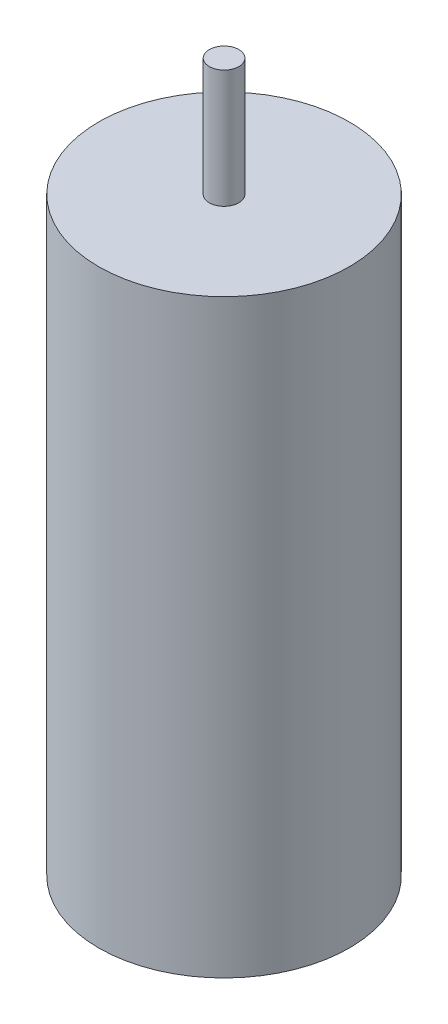
SolidWorks part; units mm, degrees
ref_plane "Front Plane" through (0, 0, 0) normal (0, 0, 1) x (1, 0, 0)
ref_plane "Top Plane" through (0, 0, 0) normal (0, 1, 0) x (1, 0, 0)
ref_plane "Right Plane" through (0, 0, 0) normal (1, 0, 0) x (0, 0, -1)
sketch "Sketch1" plane through (0, 0, 0) normal (0, 1, 0) x (1, 0, 0)
  circle A0 centre (0, 0) radius 4.25
extrude "Boss-Extrude1" add sketch "Sketch1" along normal blind 20
sketch "Sketch2" plane through (0, 20, 0) normal (0, 1, 0) x (1, 0, 0)
  circle A0 centre (0, 0) radius 0.5
extrude "Boss-Extrude2" add sketch "Sketch2" along normal blind 4
sketch3d "URDF Reference"
  line L0 (0, 0, 0) -> (10, 0, 0) construction
  line L1 (0, 0, 0) -> (0, 0, -10) construction
  point P0 (0, 0, 0)
  point P1 (0, 0, 0)
